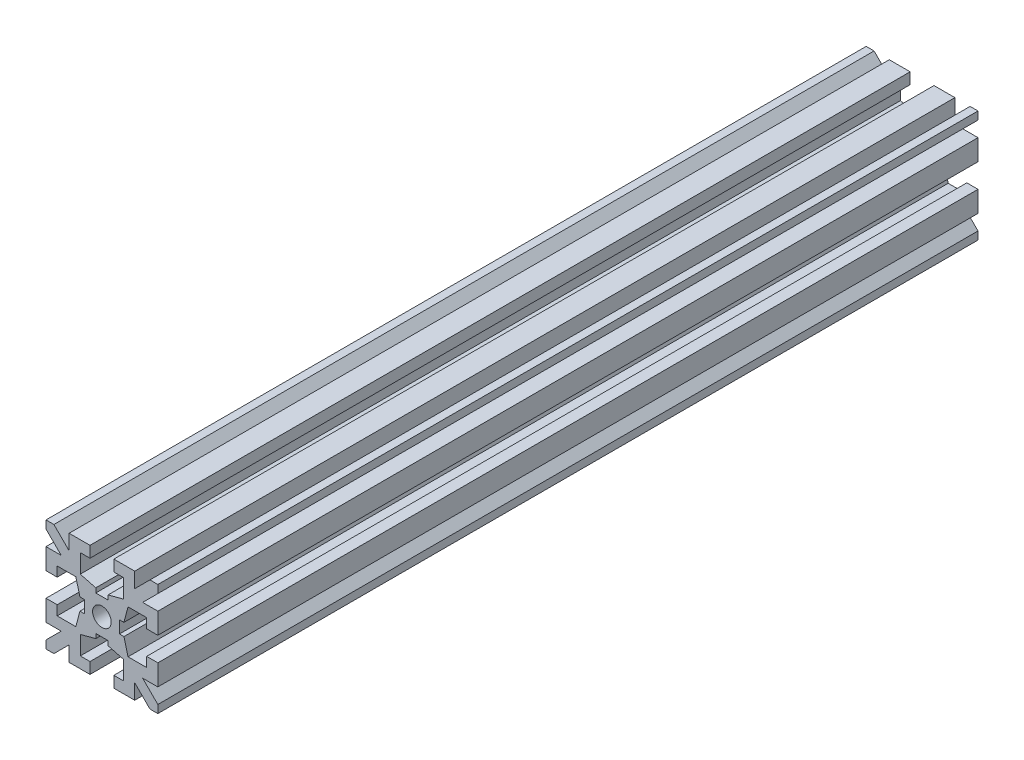
SolidWorks part; units mm, degrees
material "3.0205 (EN-AW 1200)"
ref_plane "Plano frontal" through (0, 0, 0) normal (0, 0, 1) x (1, 0, 0)
ref_plane "Plano superior" through (0, 0, 0) normal (0, 1, 0) x (1, 0, 0)
ref_plane "Plano direito" through (0, 0, 0) normal (1, 0, 0) x (0, 0, -1)
sketch "Esboço1" plane through (0, 0, 0) normal (0, 0, 1) x (1, 0, 0)
  line L0 (-25.7554, 0) -> (0, 0) construction
  line L1 (0, 0) -> (0, 21.5914) construction
  line L2 (0, 2.35) -> (-0.825, 2.35)
  line L3 (-0.825, 2.35) -> (-0.825, 2.95)
  line L4 (-0.825, 2.95) -> (-2.9, 3.5)
  line L5 (-2.9, 3.5) -> (-2.9, 6)
  line L6 (-2.9, 6) -> (-1.6, 6)
  line L7 (-1.6, 6) -> (-1.6, 7.5)
  line L8 (-1.6, 7.5) -> (-4.4, 7.5)
  line L9 (-4.4, 7.5) -> (-4.4, 5.4607)
  line L10 (-4.4, 5.4607) -> (-6.4393, 7.5)
  line L11 (-6.4393, 7.5) -> (-7.5, 7.5)
  line L12 (-7.5, 7.5) -> (0, 0) construction
  line L13 (-2.35, 0) -> (-2.35, 0.825)
  line L14 (-7.5, 6.4393) -> (-7.5, 7.5)
  line L15 (-5.4607, 4.4) -> (-7.5, 6.4393)
  line L16 (-7.5, 4.4) -> (-5.4607, 4.4)
  line L17 (-7.5, 1.6) -> (-7.5, 4.4)
  line L18 (-6, 1.6) -> (-7.5, 1.6)
  line L19 (-6, 2.9) -> (-6, 1.6)
  line L20 (-3.5, 2.9) -> (-6, 2.9)
  line L21 (-2.95, 0.825) -> (-3.5, 2.9)
  line L22 (-2.35, 0.825) -> (-2.95, 0.825)
  line L23 (-2.35, 0) -> (0, 0)
  line L24 (0, 0) -> (0, 2.35)
  dimension "D1" = 45
  dimension "D2" = 4.7
  dimension "D3" = 5.8
  dimension "D4" = 15
  dimension "D5" = 3.1
  dimension "D6" = 3.2
  dimension "D7" = 0.6
  dimension "D8" = 1.65
  dimension "D9" = 1.5
  dimension "D10" = 2.5
  dimension "D11" = 1.5
extrude "Ressalto-extrusão1" add sketch "Esboço1" along normal mid plane 110
mirror "Espelhar1" about plane through (0, 0, 0) normal (0, 1, 0) of "Ressalto-extrusão1"
mirror "Espelhar2" about plane through (0, 0, 0) normal (1, 0, 0) of "Espelhar1", "Ressalto-extrusão1"
sketch "Esboço2" plane through (0, 0, 55) normal (0, 0, 1) x (1, 0, 0)
  circle A0 centre (0, 0) radius 1.25
  dimension "D1" = 2.5
extrude "Corte-extrusão1" cut sketch "Esboço2" against normal through all both and the other way through all
